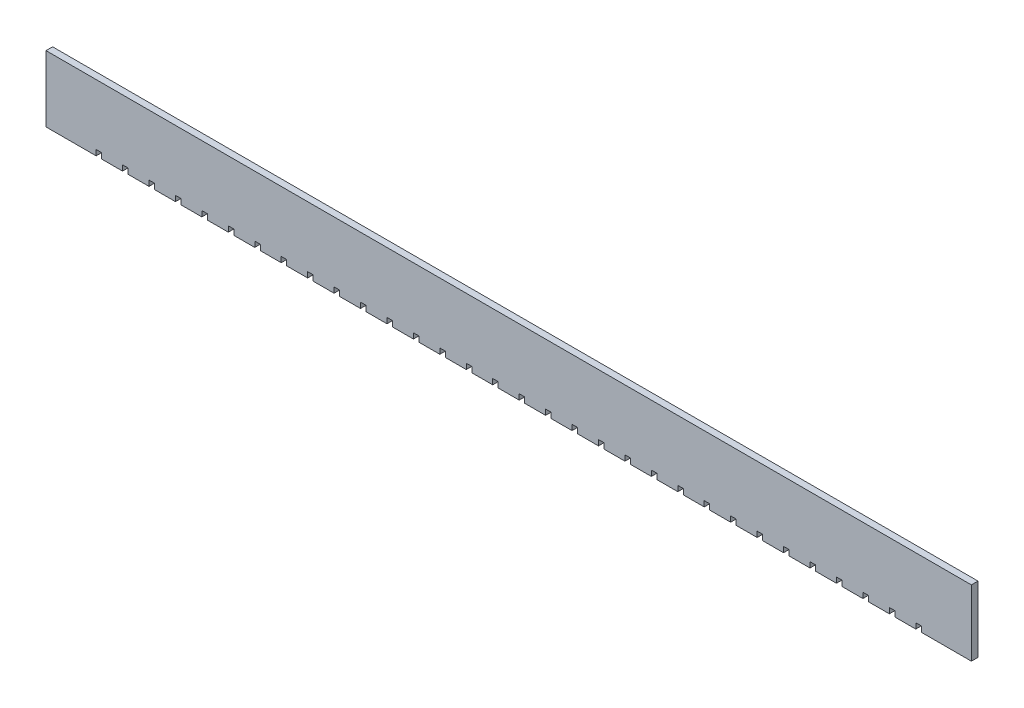
SolidWorks part; units mm, degrees
ref_plane "Front Plane" through (0, 0, 0) normal (0, 0, 1) x (1, 0, 0)
ref_plane "Top Plane" through (0, 0, 0) normal (0, 1, 0) x (1, 0, 0)
ref_plane "Right Plane" through (0, 0, 0) normal (1, 0, 0) x (0, 0, -1)
sketch "Sketch1" plane through (0, 0, 0) normal (0, 0, 1) x (1, 0, 0)
  line L0 (0, 0) -> (0, 15)
  line L1 (0, 15) -> (210, 15)
  line L2 (0, 0) -> (11.375, 0)
  line L3 (11.375, 0) -> (11.375, 1.25)
  line L4 (11.375, 1.25) -> (12.625, 1.25)
  line L5 (12.625, 1.25) -> (12.625, 0)
  line L6 (12.625, 0) -> (17.375, 0)
  line L7 (17.375, 0) -> (17.375, 1.25)
  line L8 (17.375, 1.25) -> (18.625, 1.25)
  line L9 (18.625, 1.25) -> (18.625, 0)
  line L10 (18.625, 0) -> (23.375, 0)
  line L11 (23.375, 0) -> (23.375, 1.25)
  line L12 (23.375, 1.25) -> (24.625, 1.25)
  line L13 (24.625, 1.25) -> (24.625, 0)
  line L14 (24.625, 0) -> (29.375, 0)
  line L15 (29.375, 0) -> (29.375, 1.25)
  line L16 (29.375, 1.25) -> (30.625, 1.25)
  line L17 (30.625, 1.25) -> (30.625, 0)
  line L18 (30.625, 0) -> (35.375, 0)
  line L19 (35.375, 0) -> (35.375, 1.25)
  line L20 (35.375, 1.25) -> (36.625, 1.25)
  line L21 (36.625, 1.25) -> (36.625, 0)
  line L22 (36.625, 0) -> (41.375, 0)
  line L23 (41.375, 0) -> (41.375, 1.25)
  line L24 (41.375, 1.25) -> (42.625, 1.25)
  line L25 (42.625, 1.25) -> (42.625, 0)
  line L26 (42.625, 0) -> (47.375, 0)
  line L27 (47.375, 0) -> (47.375, 1.25)
  line L28 (47.375, 1.25) -> (48.625, 1.25)
  line L29 (48.625, 1.25) -> (48.625, 0)
  line L30 (48.625, 0) -> (53.375, 0)
  line L31 (53.375, 0) -> (53.375, 1.25)
  line L32 (53.375, 1.25) -> (54.625, 1.25)
  line L33 (54.625, 1.25) -> (54.625, 0)
  line L34 (54.625, 0) -> (59.375, 0)
  line L35 (59.375, 0) -> (59.375, 1.25)
  line L36 (59.375, 1.25) -> (60.625, 1.25)
  line L37 (60.625, 1.25) -> (60.625, 0)
  line L38 (60.625, 0) -> (65.375, 0)
  line L39 (65.375, 0) -> (65.375, 1.25)
  line L40 (65.375, 1.25) -> (66.625, 1.25)
  line L41 (66.625, 1.25) -> (66.625, 0)
  line L42 (66.625, 0) -> (71.375, 0)
  line L43 (71.375, 0) -> (71.375, 1.25)
  line L44 (71.375, 1.25) -> (72.625, 1.25)
  line L45 (72.625, 1.25) -> (72.625, 0)
  line L46 (72.625, 0) -> (77.375, 0)
  line L47 (77.375, 0) -> (77.375, 1.25)
  line L48 (77.375, 1.25) -> (78.625, 1.25)
  line L49 (78.625, 1.25) -> (78.625, 0)
  line L50 (78.625, 0) -> (83.375, 0)
  line L51 (83.375, 0) -> (83.375, 1.25)
  line L52 (83.375, 1.25) -> (84.625, 1.25)
  line L53 (84.625, 1.25) -> (84.625, 0)
  line L54 (84.625, 0) -> (89.375, 0)
  line L55 (89.375, 0) -> (89.375, 1.25)
  line L56 (89.375, 1.25) -> (90.625, 1.25)
  line L57 (90.625, 1.25) -> (90.625, 0)
  line L58 (90.625, 0) -> (95.375, 0)
  line L59 (95.375, 0) -> (95.375, 1.25)
  line L60 (95.375, 1.25) -> (96.625, 1.25)
  line L61 (96.625, 1.25) -> (96.625, 0)
  line L62 (96.625, 0) -> (101.375, 0)
  line L63 (101.375, 0) -> (101.375, 1.25)
  line L64 (101.375, 1.25) -> (102.625, 1.25)
  line L65 (102.625, 1.25) -> (102.625, 0)
  line L66 (102.625, 0) -> (107.375, 0)
  line L67 (107.375, 0) -> (107.375, 1.25)
  line L68 (107.375, 1.25) -> (108.625, 1.25)
  line L69 (108.625, 1.25) -> (108.625, 0)
  line L70 (108.625, 0) -> (113.375, 0)
  line L71 (113.375, 0) -> (113.375, 1.25)
  line L72 (113.375, 1.25) -> (114.625, 1.25)
  line L73 (114.625, 1.25) -> (114.625, 0)
  line L74 (114.625, 0) -> (119.375, 0)
  line L75 (119.375, 0) -> (119.375, 1.25)
  line L76 (119.375, 1.25) -> (120.625, 1.25)
  line L77 (120.625, 1.25) -> (120.625, 0)
  line L78 (120.625, 0) -> (125.375, 0)
  line L79 (125.375, 0) -> (125.375, 1.25)
  line L80 (125.375, 1.25) -> (126.625, 1.25)
  line L81 (126.625, 1.25) -> (126.625, 0)
  line L82 (126.625, 0) -> (131.375, 0)
  line L83 (131.375, 0) -> (131.375, 1.25)
  line L84 (131.375, 1.25) -> (132.625, 1.25)
  line L85 (132.625, 1.25) -> (132.625, 0)
  line L86 (132.625, 0) -> (137.375, 0)
  line L87 (137.375, 0) -> (137.375, 1.25)
  line L88 (137.375, 1.25) -> (138.625, 1.25)
  line L89 (138.625, 1.25) -> (138.625, 0)
  line L90 (138.625, 0) -> (143.375, 0)
  line L91 (143.375, 0) -> (143.375, 1.25)
  line L92 (143.375, 1.25) -> (144.625, 1.25)
  line L93 (144.625, 1.25) -> (144.625, 0)
  line L94 (144.625, 0) -> (149.375, 0)
  line L95 (149.375, 0) -> (149.375, 1.25)
  line L96 (149.375, 1.25) -> (150.625, 1.25)
  line L97 (150.625, 1.25) -> (150.625, 0)
  line L98 (150.625, 0) -> (155.375, 0)
  line L99 (155.375, 0) -> (155.375, 1.25)
  line L100 (155.375, 1.25) -> (156.625, 1.25)
  line L101 (156.625, 1.25) -> (156.625, 0)
  line L102 (156.625, 0) -> (161.375, 0)
  line L103 (161.375, 0) -> (161.375, 1.25)
  line L104 (161.375, 1.25) -> (162.625, 1.25)
  line L105 (162.625, 1.25) -> (162.625, 0)
  line L106 (162.625, 0) -> (167.375, 0)
  line L107 (167.375, 0) -> (167.375, 1.25)
  line L108 (167.375, 1.25) -> (168.625, 1.25)
  line L109 (168.625, 1.25) -> (168.625, 0)
  line L110 (168.625, 0) -> (173.375, 0)
  line L111 (173.375, 0) -> (173.375, 1.25)
  line L112 (173.375, 1.25) -> (174.625, 1.25)
  line L113 (174.625, 1.25) -> (174.625, 0)
  line L114 (174.625, 0) -> (179.375, 0)
  line L115 (179.375, 0) -> (179.375, 1.25)
  line L116 (179.375, 1.25) -> (180.625, 1.25)
  line L117 (180.625, 1.25) -> (180.625, 0)
  line L118 (180.625, 0) -> (185.375, 0)
  line L119 (185.375, 0) -> (185.375, 1.25)
  line L120 (185.375, 1.25) -> (186.625, 1.25)
  line L121 (186.625, 1.25) -> (186.625, 0)
  line L122 (186.625, 0) -> (191.375, 0)
  line L123 (191.375, 0) -> (191.375, 1.25)
  line L124 (191.375, 1.25) -> (192.625, 1.25)
  line L125 (192.625, 1.25) -> (192.625, 0)
  line L126 (192.625, 0) -> (197.375, 0)
  line L131 (197.375, 0) -> (197.375, 1.25)
  line L132 (197.375, 1.25) -> (198.625, 1.25)
  line L133 (198.625, 1.25) -> (198.625, 0)
  line L134 (198.625, 0) -> (210, 0)
  line L135 (210, 0) -> (210, 15)
  point P3 (15, 0)
  point P4 (197.4783, 0)
  point P10 (213.9055, 7.1066)
  dimension "D1" = 6
  dimension "D2" = 1.25
  dimension "D3" = 15
  dimension "D5" = 15
  dimension "D4" = 31
extrude "Boss-Extrude1" add sketch "Sketch1" along normal blind 1.5
